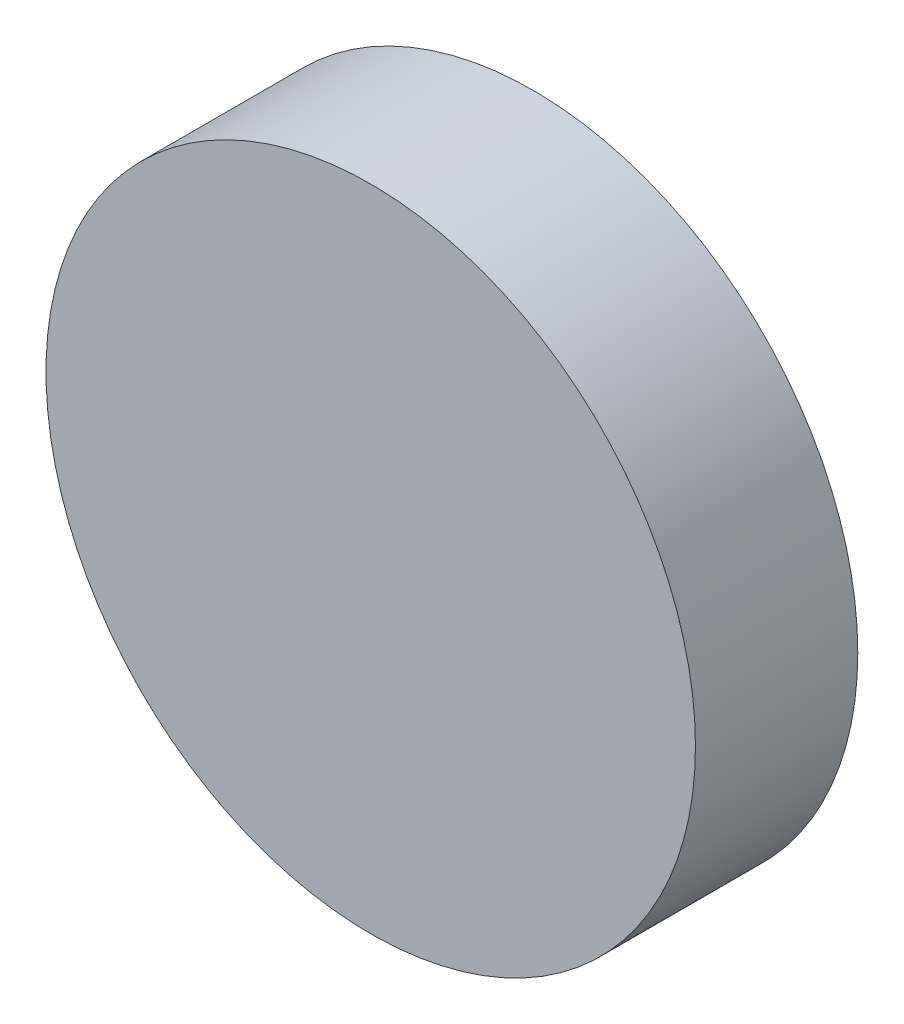
SolidWorks part; units mm, degrees
ref_plane "Front Plane" through (0, 0, 0) normal (0, 0, 1) x (1, 0, 0)
ref_plane "Top Plane" through (0, 0, 0) normal (0, 1, 0) x (1, 0, 0)
ref_plane "Right Plane" through (0, 0, 0) normal (1, 0, 0) x (0, 0, -1)
sketch "Sketch1" plane through (0, 0, 0) normal (0, 0, 1) x (1, 0, 0)
  circle A0 centre (0, 0) radius 50.8
  dimension "D1" = 101.6
extrude "Boss-Extrude1" add sketch "Sketch1" along normal blind 25.4
